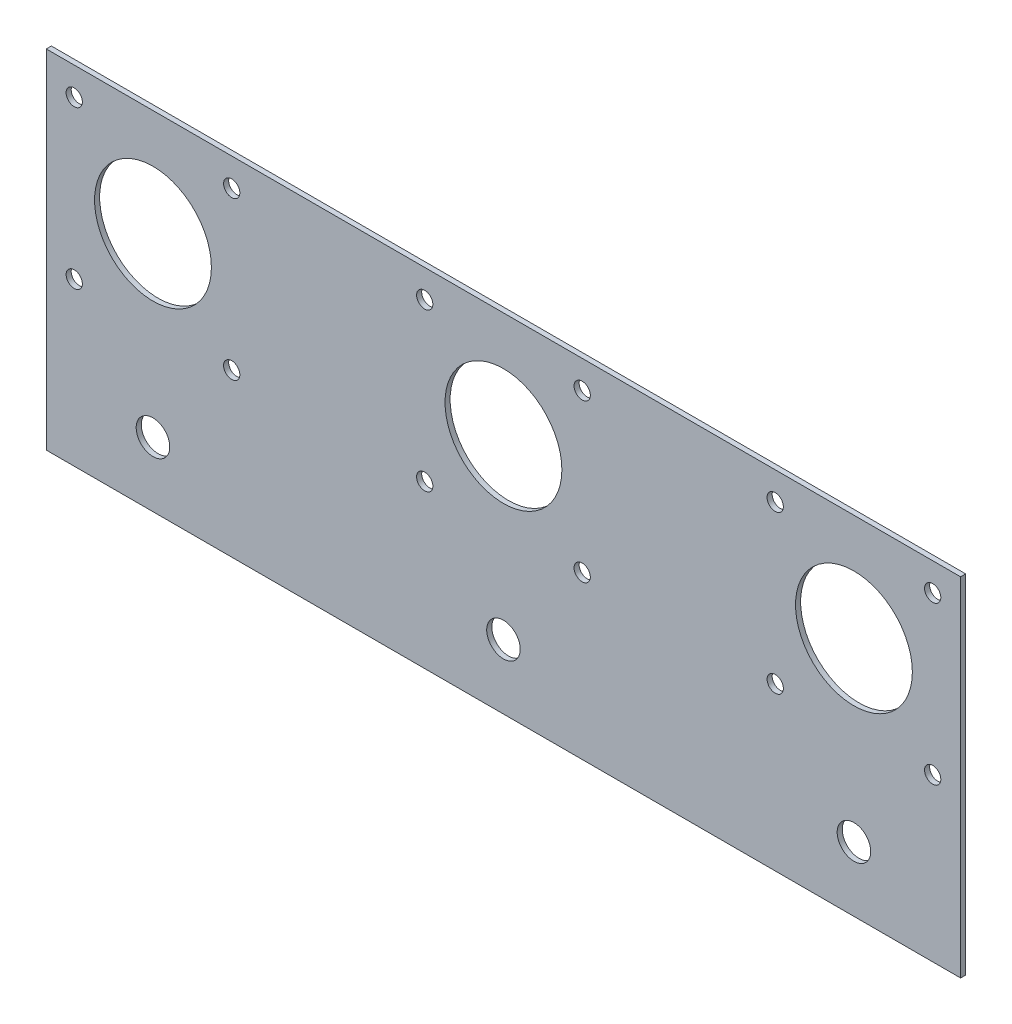
SolidWorks part; units mm, degrees
ref_plane "Front Plane" through (0, 0, 0) normal (0, 0, 1) x (1, 0, 0)
ref_plane "Top Plane" through (0, 0, 0) normal (0, 1, 0) x (1, 0, 0)
ref_plane "Right Plane" through (0, 0, 0) normal (1, 0, 0) x (0, 0, -1)
sketch "Sketch1" plane through (0, 0, 0) normal (0, 0, 1) x (1, 0, 0)
  line L0 (0, 25.4) -> (180, 25.4) construction
  line L1 (0, 0) -> (180, 0)
  line L2 (0, 0) -> (0, 68.4)
  line L3 (0, 68.4) -> (180, 68.4)
  line L4 (180, 0) -> (180, 68.4)
  line L5 (0, 12.7) -> (180, 12.7) construction
  line L6 (90, 0) -> (90, 12.7) construction
  circle A0 centre (21, 12.7) radius 3.302
  circle A1 centre (90, 12.7) radius 3.302
  circle A2 centre (159, 12.7) radius 3.302
  point P11 (109.6425, 13.5999)
  point P15 (111.849, 11.8321)
  dimension "D2" = 6.604
  dimension "D3" = 6.604
  dimension "D4" = 6.604
  dimension "D1" = 25.4
  dimension "D5" = 21
  dimension "D6" = 21
  dimension "D7" = 180
  dimension "D8" = 43
  dimension "D9" = 12.7
extrude "Boss-Extrude1" add sketch "Sketch1" along normal blind 1
sketch "Sketch2" plane through (0, 0, 1) normal (0, 0, 1) x (1, 0, 0)
  line L0 (180, 68.4) -> (0, 68.4) construction
  line L1 (36.5, 31.9) -> (5.5, 31.9) construction
  line L2 (36.5, 31.9) -> (36.5, 62.9) construction
  line L3 (36.5, 62.9) -> (5.5, 62.9) construction
  line L4 (5.5, 31.9) -> (5.5, 62.9) construction
  line L5 (36.5, 31.9) -> (5.5, 62.9) construction
  line L6 (36.5, 62.9) -> (5.5, 31.9) construction
  line L7 (0, 68.4) -> (0, 0) construction
  circle A0 centre (21, 47.4) radius 11.5
  circle A1 centre (36.5, 62.9) radius 1.6
  circle A2 centre (36.5, 31.9) radius 1.6
  circle A3 centre (5.5, 31.9) radius 1.6
  circle A4 centre (5.5, 62.9) radius 1.6
  point P0 (21, 47.4)
  dimension "D1" = 23
  dimension "D2" = 3.2
  dimension "D3" = 3.2
  dimension "D4" = 3.2
  dimension "D5" = 3.2
  dimension "D6" = 31
  dimension "D7" = 31
  dimension "D8" = 21
  dimension "D9" = 21
extrude "Cut-Extrude1" cut sketch "Sketch2" against normal blind 1
pattern_linear "LPattern1" count 3 spacing 69 along (1, 0, 0) of "Cut-Extrude1"
